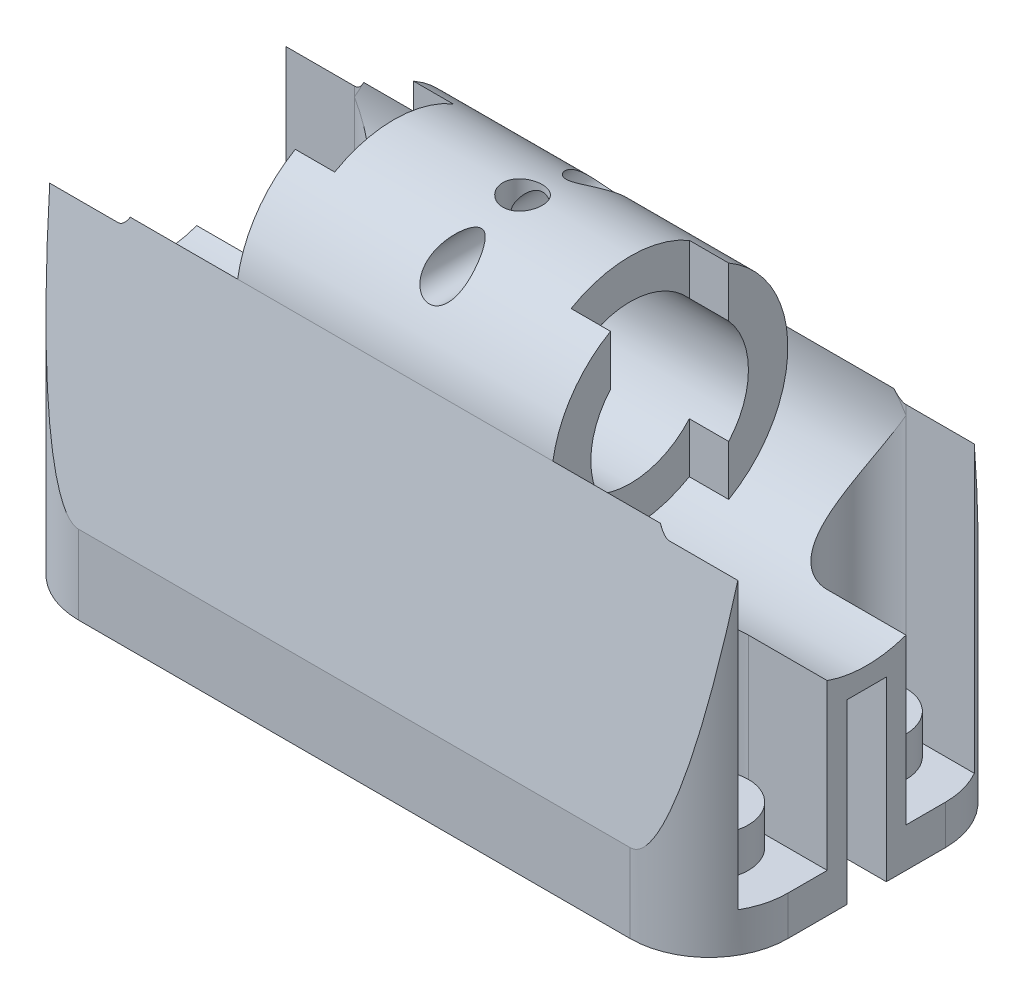
SolidWorks part; units mm, degrees
ref_plane "Front Plane" through (0, 0, 0) normal (0, 0, 1) x (1, 0, 0)
ref_plane "Top Plane" through (0, 0, 0) normal (0, 1, 0) x (1, 0, 0)
ref_plane "Right Plane" through (0, 0, 0) normal (1, 0, 0) x (0, 0, -1)
sketch "Sketch1" plane through (0, 0, 0) normal (0, 1, 0) x (1, 0, 0)
  line L1 (20, 0) -> (160, 0)
  line L2 (0, 20) -> (0, 60)
  line L3 (20, 80) -> (160, 80)
  line L4 (180, 20) -> (180, 60)
  arc A0 (20, 0) -> (0, 20) centre (20, 20) cw
  arc A1 (160, 0) -> (180, 20) centre (160, 20) ccw
  arc A2 (160, 80) -> (180, 60) centre (160, 60) cw
  arc A3 (0, 60) -> (20, 80) centre (20, 60) cw
  point P7 (0, 0)
  dimension "D1" = 20
  dimension "D2" = 140
  dimension "D3" = 40
extrude "Boss-Extrude3" add sketch "Sketch1" along normal blind 110
sketch "Sketch4" plane through (0, 110, 0) normal (0, 1, 0) x (1, 0, 0)
  line L0 (20, 50) -> (0, 50)
  line L1 (0, 60) -> (0, 20) construction
  line L3 (20, 70) -> (2.6795, 70)
  line L4 (0, 50) -> (0, 60)
  circle A1 centre (20, 60) radius 10
  arc A2 (20, 80) -> (0, 60) centre (20, 60) ccw construction
  arc A3 (2.6795, 70) -> (0, 60) centre (20, 60) ccw
  arc M7 (20, 80) -> (0, 60) centre (20, 60) ccw
  line M8 (0, 60) -> (0, 20)
  dimension "D1" = 20
  dimension "D2" = 10
extrude "Cut-Extrude3" cut sketch "Sketch4" against normal blind 90 contours A1 L3 L0 M7 M8 | A1 L4
sketch "Sketch5" plane through (0, 20, 0) normal (0, 1, 0) x (1, 0, 0)
  line L0 (20, 50) -> (0, 50)
  line L1 (0, 50) -> (0, 60)
  circle A0 centre (20, 60) radius 10
  line M2 (0, 50) -> (20, 50)
  line M4 (20, 70) -> (2.6795, 70)
  arc M5 (2.6795, 70) -> (0, 60) centre (20, 60) ccw
  line M6 (0, 60) -> (0, 50)
  dimension "D1" = 20
  dimension "D2" = 20
extrude "Cut-Extrude4" cut sketch "Sketch5" against normal blind 10 contours A0 M4 M5 M6 M2
sketch "Sketch6" plane through (0, 110, 0) normal (0, 1, 0) x (1, 0, 0)
  line L0 (20, 30) -> (0, 30)
  line L1 (0, 50) -> (0, 20) construction
  line L2 (0, 30) -> (0, 20)
  line L3 (20, 10) -> (2.6795, 10)
  line L4 (160, 70) -> (177.3205, 70)
  line L5 (160, 50) -> (180, 50)
  line L6 (180, 20) -> (180, 60) construction
  line L7 (180, 50) -> (180, 60)
  line L8 (160, 30) -> (180, 30)
  line L9 (180, 30) -> (180, 20)
  line L10 (160, 10) -> (177.3205, 10)
  circle A0 centre (20, 20) radius 10
  circle A1 centre (160, 60) radius 10
  circle A2 centre (160, 20) radius 10
  arc A3 (0, 20) -> (20, 0) centre (20, 20) ccw construction
  arc A4 (0, 20) -> (2.6795, 10) centre (20, 20) ccw
  arc A5 (180, 60) -> (160, 80) centre (160, 60) ccw construction
  arc A6 (180, 60) -> (177.3205, 70) centre (160, 60) ccw
  arc A9 (180, 20) -> (177.3205, 10) centre (160, 20) cw
  line M2 (0, 50) -> (0, 20)
  arc M3 (0, 20) -> (20, 0) centre (20, 20) ccw
  arc M5 (160, 0) -> (180, 20) centre (160, 20) ccw
  line M6 (180, 20) -> (180, 60)
  arc M7 (180, 60) -> (160, 80) centre (160, 60) ccw
  dimension "D1" = 20
  dimension "D2" = 20
  dimension "D3" = 20
  dimension "D4" = 20
  dimension "D5" = 17.3205
extrude "Cut-Extrude5" cut sketch "Sketch6" against normal blind 90 contours A0 L0 L3 M2 M3 | A0 | A1 | A1 L5 L4 M6 M7 | A2 L10 L8 M5 M6
sketch "Sketch7" plane through (0, 20, 0) normal (0, 1, 0) x (1, 0, 0)
  line L0 (20, 10) -> (2.6795, 10)
  line L1 (160, 50) -> (180, 50)
  line L2 (180, 50) -> (180, 60)
  line L3 (160, 30) -> (180, 30)
  line L4 (180, 30) -> (180, 20)
  circle A0 centre (20, 20) radius 10
  circle A1 centre (160, 60) radius 10
  circle A2 centre (160, 20) radius 10
  line M1 (2.6795, 10) -> (20, 10)
  line M3 (20, 30) -> (0, 30)
  line M4 (0, 30) -> (0, 20)
  arc M5 (0, 20) -> (2.6795, 10) centre (20, 20) ccw
  dimension "D1" = 20
  dimension "D2" = 20
  dimension "D3" = 20
  dimension "D4" = 20
extrude "Cut-Extrude6" cut sketch "Sketch7" against normal blind 10 contours A0 M3 M4 M5 M1
sketch "Sketch8" plane through (0, 20, 0) normal (0, 1, 0) x (1, 0, 0)
  line L0 (160, 50) -> (180, 50)
  line L1 (180, 50) -> (180, 60)
  line L2 (160, 70) -> (177.3205, 70)
  line L7 (180, 60) -> (180, 50)
  circle A0 centre (160, 60) radius 10
  arc A2 (177.3205, 70) -> (180, 60) centre (160, 60) cw
  line M2 (160, 50) -> (180, 50)
  line M3 (180, 50) -> (180, 60)
  arc M4 (180, 60) -> (177.3205, 70) centre (160, 60) ccw
  line M5 (177.3205, 70) -> (160, 70)
  dimension "D1" = 20
  dimension "D3" = 20
  dimension "D4" = 17.3205
  dimension "D5" = 17.3205
  dimension "D6" = 10
extrude "Cut-Extrude7" cut sketch "Sketch8" against normal blind 10 contours A0 M2 M3 M4 M5
sketch "Sketch9" plane through (0, 20, 0) normal (0, 1, 0) x (1, 0, 0)
  line L0 (160, 30) -> (180, 30)
  line L1 (180, 30) -> (180, 20)
  line L2 (160, 10) -> (177.3205, 10)
  circle A0 centre (160, 20) radius 10
  arc A1 (180, 20) -> (177.3205, 10) centre (160, 20) cw
  line M1 (160, 10) -> (177.3205, 10)
  arc M2 (177.3205, 10) -> (180, 20) centre (160, 20) ccw
  line M3 (180, 20) -> (180, 30)
  line M4 (180, 30) -> (160, 30)
  dimension "D1" = 20
  dimension "D2" = 17.3205
extrude "Cut-Extrude8" cut sketch "Sketch9" against normal blind 10 contours A0 M1 M2 M3 M4
ref_plane "Plane1" through (50, 0, 0) normal (1, 0, 0) x (0, 0, -1)
sketch "Sketch10" plane through (50, 0, 0) normal (1, 0, 0) x (0, 0, -1)
  line L0 (80, 20) -> (69.6219, 84.7479)
  line L1 (10.3781, 84.7479) -> (0, 20)
  line L2 (60, 0) -> (80, 0) construction
  line L3 (80, 20) -> (80, 110)
  line L4 (80, 110) -> (0, 110)
  line L5 (0, 110) -> (0, 20)
  circle A0 centre (40, 80) radius 30
  dimension "D1" = 60
  dimension "D2" = 30
  dimension "D3" = 40
  dimension "D4" = 20
  dimension "D5" = 80
  dimension "D6" = 20
  dimension "D7" = 80
extrude "Cut-Extrude11" cut sketch "Sketch10" against normal blind 165 and the other way blind 159 contours A0 L0 L3 L4 | A0 L4 L5 L1
sketch "Sketch11" plane through (50, 0, 0) normal (1, 0, 0) x (0, 0, -1)
  circle A0 centre (40, 80) radius 30
  dimension "D1" = 60
extrude "Cut-Extrude12" cut sketch "Sketch11" against normal blind 165
ref_plane "Plane2" through (130, 0, 0) normal (1, 0, 0) x (0, 0, -1)
sketch "Sketch12" plane through (130, 0, 0) normal (1, 0, 0) x (0, 0, -1)
  circle A0 centre (40, 80) radius 30
  dimension "D1" = 60
extrude "Cut-Extrude13" cut sketch "Sketch12" along normal blind 165
sketch "Sketch13" plane through (50, 0, 0) normal (-1, 0, 0) x (0, 0, 1)
  line L0 (-55, 54.0192) -> (-55, 105.9808)
  line L1 (-25, 54.0192) -> (-25, 105.9808)
  arc A0 (-55, 54.0192) -> (-25, 54.0192) centre (-40, 80) ccw
  arc A1 (-69.6219, 84.7479) -> (-10.3781, 84.7479) centre (-40, 80) ccw construction
  arc A2 (-10.3781, 84.7479) -> (-69.6219, 84.7479) centre (-40, 80) ccw construction
  arc A3 (-55, 105.9808) -> (-25, 105.9808) centre (-40, 80) cw
  arc M1 (-10.3781, 84.7479) -> (-69.6219, 84.7479) centre (-40, 80) ccw
  arc M2 (-69.6219, 84.7479) -> (-10.3781, 84.7479) centre (-40, 80) ccw
  dimension "D1" = 15
  dimension "D2" = 15
extrude "Cut-Extrude14" cut sketch "Sketch13" against normal blind 10 contours L1 L0 M2 M1
sketch "Sketch14" plane through (130, 0, 0) normal (1, 0, 0) x (0, 0, -1)
  line L0 (25, 54.0192) -> (25, 105.9808)
  line L1 (55, 54.0192) -> (55, 105.9808)
  arc A0 (55, 54.0192) -> (25, 54.0192) centre (40, 80) cw
  arc A1 (10.3781, 84.7479) -> (69.6219, 84.7479) centre (40, 80) ccw construction
  arc A2 (69.6219, 84.7479) -> (10.3781, 84.7479) centre (40, 80) ccw construction
  arc A3 (25, 105.9808) -> (55, 105.9808) centre (40, 80) cw
  dimension "D1" = 15
  dimension "D2" = 15
extrude "Cut-Extrude15" cut sketch "Sketch14" against normal blind 10 contours A3 L0 A0 L1
sketch "Sketch15" plane through (50, 0, 0) normal (-1, 0, 0) x (0, 0, 1)
  circle A0 centre (-40, 80) radius 20
  dimension "D1" = 40
extrude "Cut-Extrude16" cut sketch "Sketch15" against normal blind 91
sketch "Sketch16" plane through (0, 0, 0) normal (0, -1, 0) x (1, 0, 0)
  circle A0 centre (92.6795, -40) radius 5
  dimension "D1" = 10
  dimension "D2" = 90
  dimension "D3" = 40
extrude "Cut-Extrude17" cut sketch "Sketch16" against normal blind 157
ref_plane "Plane4" through (93, 0, 0) normal (1, 0, 0) x (0, 0, -1)
sketch "Sketch17" plane through (130, 0, 0) normal (1, 0, 0) x (0, 0, -1)
  line L1 (35, 45) -> (45, 45)
  line L2 (45, 45) -> (45, 0)
  line L3 (45, 0) -> (35, 0)
  line L4 (35, 45) -> (35, 0)
  dimension "D1" = 10
  dimension "D2" = 0
  dimension "D3" = 35
  dimension "D4" = 45
  dimension "D5" = 45
extrude "Cut-Extrude20" cut sketch "Sketch17" against normal blind 157 and the other way blind 157
sketch "Sketch19" plane through (0, 0, 0) normal (0, 0, 1) x (1, 0, 0)
  circle A0 centre (93, 103) radius 5
  dimension "D1" = 10
  dimension "D2" = 87
  dimension "D3" = 7
extrude "Cut-Extrude23" cut sketch "Sketch19" against normal blind 157
